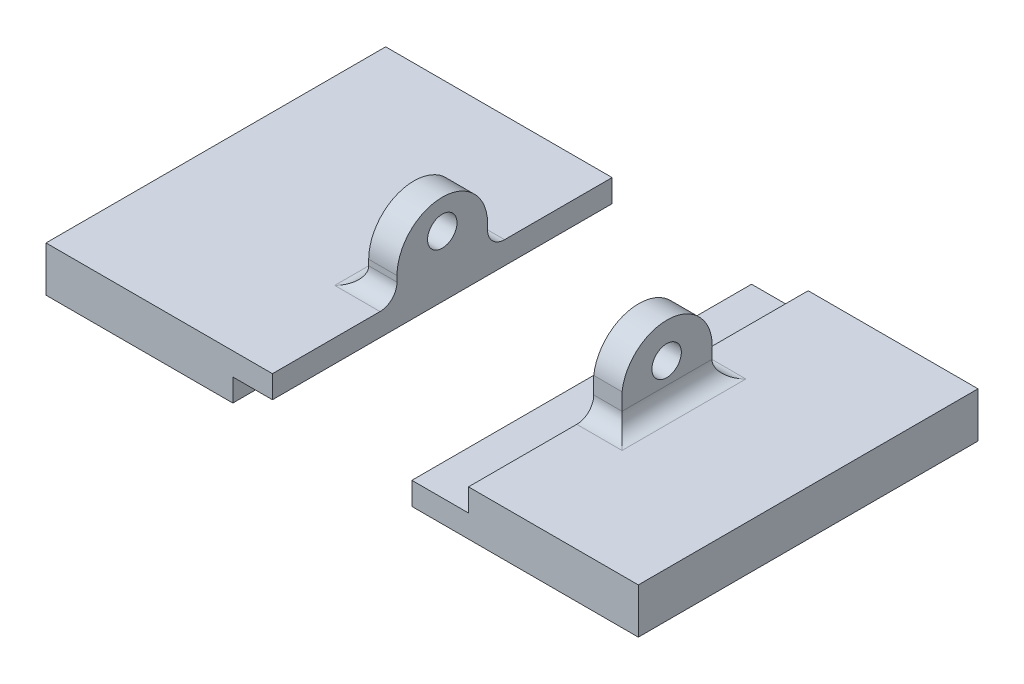
SolidWorks part; units mm, degrees
ref_plane "Front Plane" through (0, 0, 0) normal (0, 0, 1) x (1, 0, 0)
ref_plane "Top Plane" through (0, 0, 0) normal (0, 1, 0) x (1, 0, 0)
ref_plane "Right Plane" through (0, 0, 0) normal (1, 0, 0) x (0, 0, -1)
sketch "Sketch1" plane through (0, 0, 0) normal (0, 1, 0) x (1, 0, 0)
  line L1 (0, 12.1168) -> (-20, 12.1168)
  line L2 (0, 12.1168) -> (0, -17.8832)
  line L3 (0, -17.8832) -> (-20, -17.8832)
  line L4 (-20, 12.1168) -> (-20, -17.8832)
  line L5 (12.3136, 12.1168) -> (32.3136, 12.1168)
  line L6 (12.3136, 12.1168) -> (12.3136, -17.8832)
  line L7 (12.3136, -17.8832) -> (32.3136, -17.8832)
  line L8 (32.3136, 12.1168) -> (32.3136, -17.8832)
  dimension "D1" = 20
  dimension "D2" = 30
  dimension "D3" = 20
  dimension "D4" = 30
extrude "Boss-Extrude2" add sketch "Sketch1" along normal blind 4
sketch "Sketch2" plane through (0, 0, 0) normal (1, 0, 0) x (0, 0, -1)
  line L0 (-17.8832, 4) -> (-17.8832, 0) construction
  line L1 (12.1168, 0) -> (-17.8832, 0)
  line L2 (12.1168, 0) -> (12.1168, 2)
  line L3 (12.1168, 2) -> (-17.8832, 2)
  line L4 (-17.8832, 0) -> (-17.8832, 2)
extrude "Cut-Extrude1" cut sketch "Sketch2" against normal blind 3.5
sketch "Sketch3" plane through (12.3136, 0, 0) normal (-1, 0, 0) x (0, 0, 1)
  line L0 (17.8832, 4) -> (17.8832, 0) construction
  line L1 (-12.1168, 4) -> (17.8832, 4)
  line L2 (-12.1168, 4) -> (-12.1168, 2)
  line L3 (-12.1168, 2) -> (17.8832, 2)
  line L4 (17.8832, 4) -> (17.8832, 2)
extrude "Cut-Extrude2" cut sketch "Sketch3" against normal blind 5
sketch "Sketch4" plane through (0, 0, 0) normal (1, 0, 0) x (0, 0, -1)
  line L0 (-17.8832, 4) -> (12.1168, 4) construction
  line L1 (-6.8832, 4) -> (1.1168, 4)
  line L2 (-6.8832, 4) -> (-6.8832, 6)
  line L4 (1.1168, 4) -> (1.1168, 6)
  line L5 (12.1168, 4) -> (12.1168, 2) construction
  arc A1 (1.1168, 6) -> (-6.8832, 6) centre (-2.8832, 6) ccw
  circle A2 centre (-2.8832, 7.4) radius 1.3
  dimension "D4" = 2.6
  dimension "D1" = 8
  dimension "D2" = 2
  dimension "D3" = 11
  dimension "D5" = 3.4
extrude "Boss-Extrude3" add sketch "Sketch4" against normal blind 2.5
sketch "Sketch5" plane through (17.3136, 0, 0) normal (-1, 0, 0) x (0, 0, 1)
  line L0 (17.8832, 4) -> (-12.1168, 4) construction
  line L1 (-1.1168, 4) -> (6.8214, 4)
  line L2 (-1.1168, 4) -> (-1.1168, 6)
  line L4 (6.8214, 4) -> (6.8214, 6.9923)
  line L5 (-12.1168, 4) -> (-12.1168, 2) construction
  arc A1 (6.8214, 6.9923) -> (-1.1168, 6) centre (2.8523, 6.4961) ccw
  circle A2 centre (2.8832, 7.4) radius 1.3
  dimension "D4" = 2.6
  dimension "D5" = 3.4
  dimension "D1" = 2
  dimension "D2" = 8
  dimension "D3" = 11
extrude "Boss-Extrude4" add sketch "Sketch5" against normal blind 2.5
fillet "Fillet1" radius 1.5 3 edges at (-1.25, 4, -1.1168) (-2.5, 4, 2.8832) (-1.25, 4, 6.8832)
fillet "Fillet2" radius 1.5 3 edges at (18.5636, 4, 6.8214) (19.8136, 4, 2.8523) (18.5636, 4, -1.1168)
